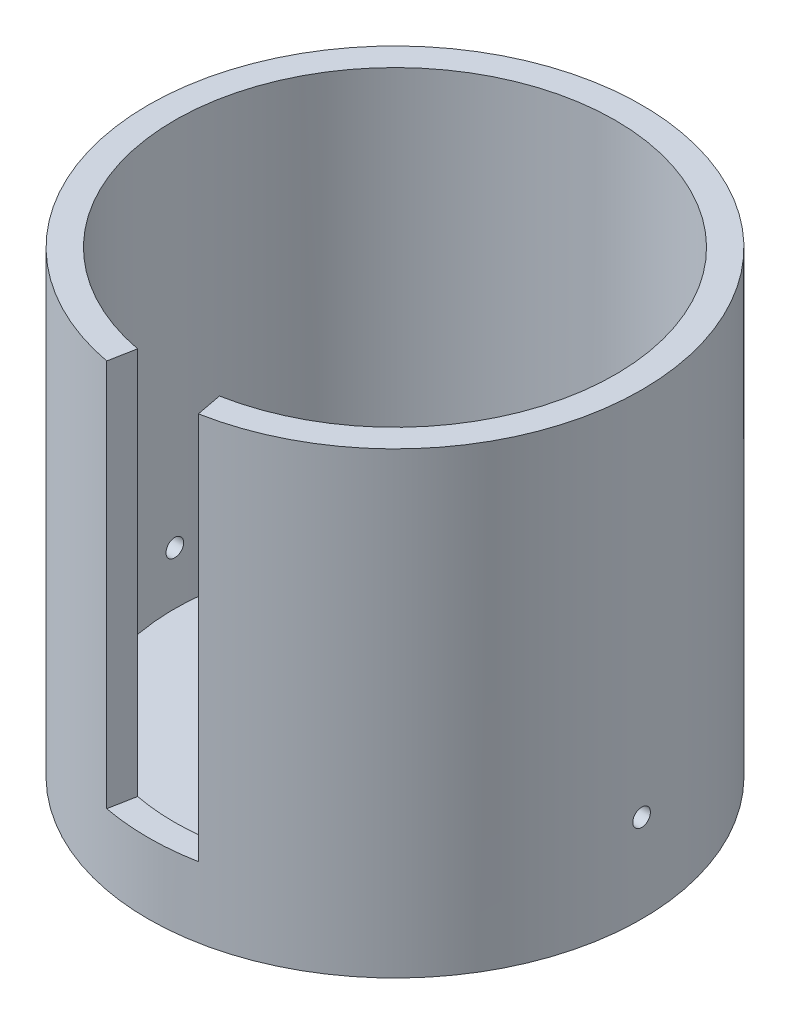
SolidWorks part; units mm, degrees
ref_plane "Спереди" through (0, 0, 0) normal (0, 0, 1) x (1, 0, 0)
ref_plane "Сверху" through (0, 0, 0) normal (0, 1, 0) x (1, 0, 0)
ref_plane "Справа" through (0, 0, 0) normal (1, 0, 0) x (0, 0, -1)
sketch "исходное дно" plane through (0, 0, 0) normal (0, 1, 0) x (1, 0, 0)
  circle A0 centre (0, 0) radius 70
  dimension "D1" = 140
extrude "Бобышка-Вытянуть1" add sketch "исходное дно" along normal blind 130
sketch "вырез основной" plane through (0, 130, 0) normal (0, 1, 0) x (1, 0, 0)
  circle A0 centre (0, 0) radius 62.5
  dimension "D1" = 125
extrude "Вырез-Вытянуть1" cut sketch "вырез основной" against normal blind 120
sketch "вырез под ручку" plane through (0, 130, 0) normal (0, 1, 0) x (1, 0, 0)
  line L0 (0, 0) -> (0, -74.0341) construction
  line L1 (-11.6071, -61.4127) -> (-13, -68.7823)
  line L2 (0, 0) -> (13, -68.7823) construction
  line L4 (11.6071, -61.4127) -> (13, -68.7823)
  line L9 (0, 0) -> (-13, -68.7823) construction
  line L10 (-11.6071, -61.4127) -> (11.6071, -61.4127)
  line L11 (-13, -68.7823) -> (0, -74.0341)
  line L12 (0, -74.0341) -> (13, -68.7823)
  circle A0 centre (0, 0) radius 70 construction
  circle A1 centre (0, 0) radius 62.5 construction
  dimension "D1" = 13
  dimension "D2" = 14.0208
extrude "Вырез-Вытянуть2" cut sketch "вырез под ручку" against normal blind 110
sketch "Эскиз5" plane through (0, 0, 0) normal (0, -1, 0) x (1, 0, 0)
  circle A0 centre (0, 0) radius 35
  dimension "D1" = 70
extrude "Вырез-Вытянуть3" cut sketch "Эскиз5" against normal blind 110
ref_plane "Плоскость4" through (70, 0, 0) normal (1, 0, 0) x (0, 0, -1)
sketch "под отверстие с кружкой" plane through (70, 0, 0) normal (1, 0, 0) x (0, 0, -1)
  line L0 (0, 0) -> (0, 110) construction
  line L1 (0, 110) -> (0, 99.1685) construction
  circle A0 centre (0, 110) radius 2.5
  dimension "D2" = 5
  dimension "D1" = 110
sketch "ось" plane through (0, 0, 0) normal (0, 0, 1) x (1, 0, 0)
  line L0 (0, -1.8897) -> (0, 309.8075) construction
sketch "Эскиз9" plane through (70, 0, 0) normal (1, 0, 0) x (0, 0, -1)
  line L0 (0, 0) -> (0, 25) construction
  circle A0 centre (0, 25) radius 2.5
  dimension "D2" = 5
  dimension "D1" = 25
extrude "Вырез-Вытянуть5" cut sketch "Эскиз9" against normal blind 30
pattern_circular "Круговой массив2" count 4 over 360 about axis through (0, -1.8897, 0) along (0, 1, 0) of "Вырез-Вытянуть5"
